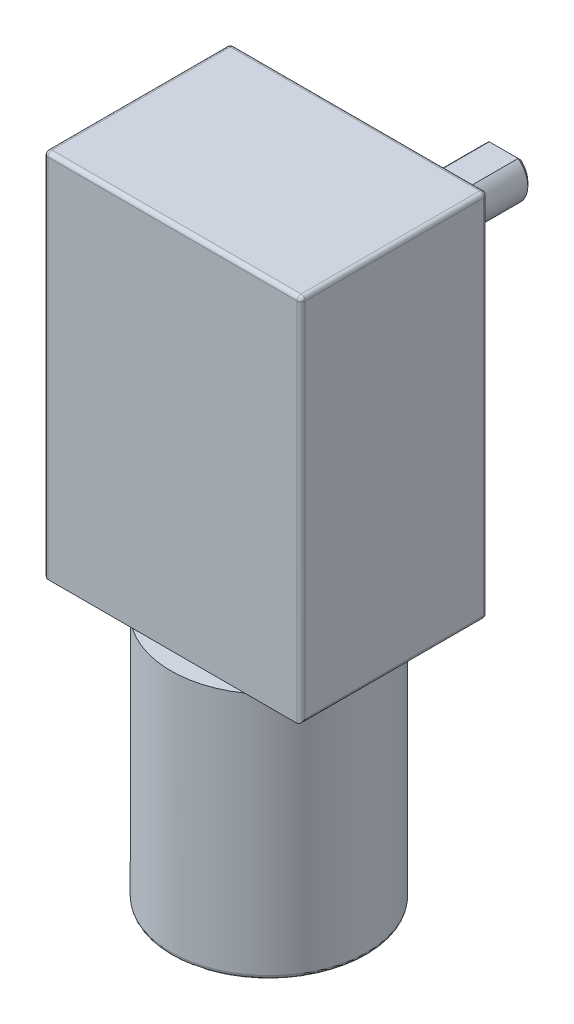
SolidWorks part; units mm, degrees
material "AISI 1020"
ref_plane "Спереди" through (0, 0, 0) normal (0, 0, 1) x (1, 0, 0)
ref_plane "Сверху" through (0, 0, 0) normal (0, 1, 0) x (1, 0, 0)
ref_plane "Справа" through (0, 0, 0) normal (1, 0, 0) x (0, 0, -1)
sketch "Эскиз1" plane through (0, 0, 0) normal (0, 1, 0) x (1, 0, 0)
  circle A0 centre (0, 0) radius 3.5
  dimension "D1" = 7
extrude "Бобышка-Вытянуть1" add sketch "Эскиз1" along normal blind 3
sketch "Эскиз2" plane through (0, 3, 0) normal (0, 1, 0) x (1, 0, 0)
  circle A0 centre (0, 0) radius 12.2
  dimension "D1" = 24.4
extrude "Бобышка-Вытянуть2" add sketch "Эскиз2" along normal blind 30.8
sketch "Эскиз3" plane through (0, 33.8, 0) normal (0, 1, 0) x (1, 0, 0)
  line L0 (0, 0) -> (2.2217, 0) construction
  line L1 (-18, 15.2) -> (14, 15.2)
  line L2 (-18, 15.2) -> (-18, -10)
  line L3 (-18, -10) -> (14, -10)
  line L4 (14, 15.2) -> (14, -10)
  dimension "D1" = 25.2
  dimension "D2" = 32
  dimension "D3" = 10
extrude "Бобышка-Вытянуть3" add sketch "Эскиз3" along normal blind 46
sketch "Эскиз4" plane through (0, 0, -15.2) normal (0, 0, -1) x (-1, 0, 0)
  line L0 (2, 79.8) -> (2, 53.9336) construction
  line L1 (-14, 79.8) -> (18, 79.8) construction
  circle A0 centre (2, 64.8) radius 3
  dimension "D2" = 6
  dimension "D1" = 15
extrude "Бобышка-Вытянуть4" add sketch "Эскиз4" along normal blind 16.5
sketch "Эскиз5" plane through (0, 0, -31.7) normal (0, 0, -1) x (-1, 0, 0)
  line L0 (0.2, 67.2) -> (3.8, 67.2)
  circle A1 centre (2, 64.8) radius 3
  arc A2 (3.8, 67.2) -> (0.2, 67.2) centre (2, 64.8) ccw
  dimension "D2" = 2.4
  dimension "D1" = 0
extrude "Вырез-Вытянуть1" cut sketch "Эскиз5" against normal blind 12
sketch "Эскиз6" plane through (0, 0, -15.2) normal (0, 0, -1) x (-1, 0, 0)
  line L0 (2, 64.8) -> (2, 84.2537) construction
  line L1 (-4.1679, 52.8) -> (8.1679, 52.8) construction
  line L2 (-4.1679, 55.8) -> (8.1679, 55.8)
  line L3 (-4.1679, 49.8) -> (8.1679, 49.8)
  line L4 (-14, 33.8) -> (18, 33.8)
  line L5 (18, 33.8) -> (18, 79.8)
  line L6 (18, 79.8) -> (-14, 79.8)
  line L7 (-14, 79.8) -> (-14, 33.8)
  line L8 (-14, 33.8) -> (18, 33.8)
  line L9 (18, 33.8) -> (18, 79.8)
  line L10 (18, 79.8) -> (-14, 79.8)
  line L11 (-14, 79.8) -> (-14, 33.8)
  circle A0 centre (11, 73.8) radius 3
  circle A1 centre (-7, 73.8) radius 3
  circle A2 centre (-7, 40.8) radius 3
  circle A3 centre (11, 40.8) radius 3
  circle A4 centre (2, 64.8) radius 6.5
  circle A5 centre (2, 64.8) radius 3
  arc A6 (-4.1679, 55.8) -> (-4.1679, 49.8) centre (-4.1679, 52.8) ccw
  arc A7 (8.1679, 49.8) -> (8.1679, 55.8) centre (8.1679, 52.8) ccw
  point P19 (2, 52.8)
  line M16 (-14, 33.8) -> (18, 33.8)
  line M17 (18, 33.8) -> (18, 79.8)
  line M18 (18, 79.8) -> (-14, 79.8)
  line M19 (-14, 79.8) -> (-14, 33.8)
  dimension "D4" = 6
  dimension "D7" = 6
  dimension "D8" = 13
  dimension "D10" = 3
  dimension "D2" = 18
  dimension "D3" = 6
  dimension "D5" = 18
  dimension "D6" = 33
  dimension "D9" = 12
  dimension "D1" = 0
extrude "Вырез-Вытянуть2" cut sketch "Эскиз6" against normal blind 2 contours A7 L3 A6 L2 A4 A3 A2 A1 A0 M19 M16 M17 M18
fillet "Скругление1" radius 0.5 10 edges at (7.1679, 52.8, -15.2) (-2, 49.8, -15.2) (-11.1679, 52.8, -15.2) (4, 40.8, -15.2) (-8.5, 64.8, -15.2) (-8.5, 64.8, -13.2) (-14, 40.8, -13.2) (-14, 73.8, -15.2) (4, 73.8, -15.2) (-2, 55.8, -15.2)
chamfer "Фаска1" distance 0.5 angle 45 1 edges at (-2, 61.8, -31.7)
chamfer "Фаска2" distance 0.5 angle 45 1 edges at (-2, 67.2, -31.7)
sketch "Эскиз7" plane through (0, 0, -15.2) normal (0, 0, -1) x (-1, 0, 0)
  circle A0 centre (11, 73.8) radius 1.6
  circle A1 centre (-7, 73.8) radius 1.6
  circle A2 centre (-7, 40.8) radius 1.6
  circle A3 centre (11, 40.8) radius 1.6
  dimension "D1" = 3.2
extrude "Вырез-Вытянуть3" cut sketch "Эскиз7" against normal blind 4
fillet "Скругление2" radius 0.5 13 edges at (-18, 79.8, -1.6) (-18, 56.8, 10) (-18, 33.8, -1.6) (-18, 56.8, -13.2) (0, 0, 3.5) (0, 3, 12.2) (14, 33.8, -1.6) (14, 56.8, 10) (14, 56.8, -13.2) (-2, 33.8, -13.2) (-2, 79.8, 10) (-2, 79.8, -13.2) (14, 79.8, -1.6)
